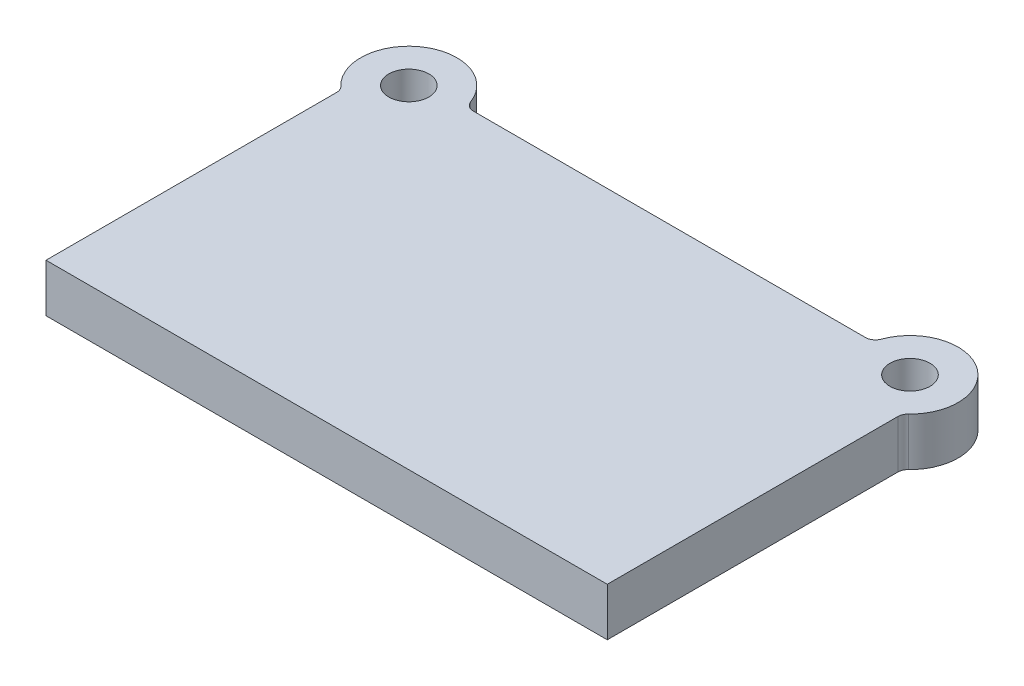
SolidWorks part; units mm, degrees
ref_plane "Front Plane" through (0, 0, 0) normal (0, 0, 1) x (1, 0, 0)
ref_plane "Top Plane" through (0, 0, 0) normal (0, 1, 0) x (1, 0, 0)
ref_plane "Right Plane" through (0, 0, 0) normal (1, 0, 0) x (0, 0, -1)
sketch "Sketch1" plane through (0, 0, 0) normal (0, 1, 0) x (1, 0, 0)
  line L0 (280, 0) -> (-280, 0)
  line L1 (-280, 0) -> (-280, 294.53)
  line L2 (0, 0) -> (0, 342) construction
  line L3 (203.0532, 342) -> (-203.0532, 342)
  line L4 (280, 0) -> (280, 294.53)
  arc A0 (-203.0532, 342) -> (-280, 294.53) centre (-250, 332) ccw
  circle A1 centre (-250, 332) radius 20
  circle A2 centre (250, 332) radius 20
  arc A3 (203.0532, 342) -> (280, 294.53) centre (250, 332) cw
  point P9 (-217.3953, 320.7907)
  point P10 (-258.0465, 265.1233)
  point P11 (-151.8092, 342)
  dimension "D3" = 96
  dimension "D4" = 40
  dimension "D1" = 342
  dimension "D2" = 332
  dimension "D5" = 560
  dimension "D6" = 500
extrude "Boss-Extrude1" add sketch "Sketch1" along normal blind 48
fillet "Fillet1" radius 10 4 edges at (-280, 24, -294.53) (-203.0532, 24, -342) (203.0532, 24, -342) (280, 24, -294.53)
